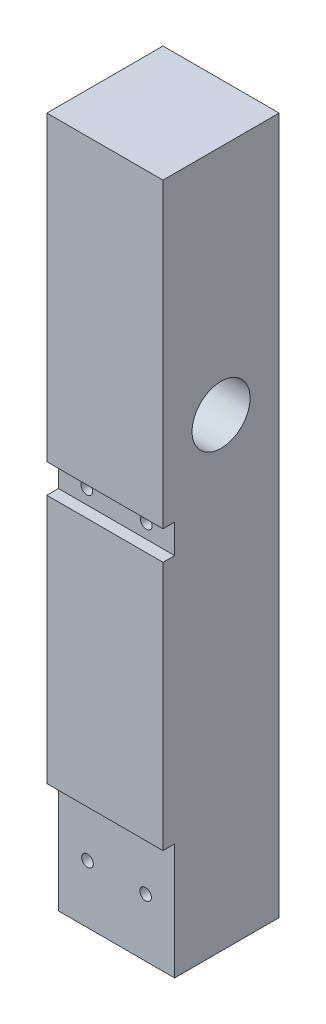
SolidWorks part; units mm, degrees
ref_plane "Front Plane" through (0, 0, 0) normal (0, 0, 1) x (1, 0, 0)
ref_plane "Top Plane" through (0, 0, 0) normal (0, 1, 0) x (1, 0, 0)
ref_plane "Right Plane" through (0, 0, 0) normal (1, 0, 0) x (0, 0, -1)
sketch "Sketch1" plane through (0, 0, 0) normal (1, 0, 0) x (0, 0, -1)
  line L0 (0, 55) -> (0, -55) construction
  line L1 (0, 120) -> (20, 120)
  line L2 (0, 120) -> (0, 0)
  line L3 (0, 0) -> (20, 0)
  line L4 (20, 120) -> (20, 0)
  line L5 (55, 0) -> (-55, 0) construction
  circle A2 centre (10, 80) radius 2.5
  dimension "D3" = 5
  dimension "D4" = 40
  dimension "D5" = 10
  dimension "D1" = 20
  dimension "D2" = 120
extrude "Boss-Extrude2" add sketch "Sketch1" against normal blind 20
ref_plane "Plane1" through (0, 0, 0) normal (1, 0, 0) x (0, 0, -1)
sketch "Sketch10" plane through (0, 0, 0) normal (1, 0, 0) x (0, 0, -1)
  circle A0 centre (10, 80) radius 5
  dimension "D1" = 10
extrude "Cut-Extrude1" cut sketch "Sketch10" against normal blind 10
ref_plane "Plane2" through (0, 0, 0) normal (0, 0, 1) x (1, 0, 0)
sketch "Sketch11" plane through (0, 0, 0) normal (0, 0, 1) x (1, 0, 0)
  line L0 (-10, 120) -> (-10, 0)
  line L1 (-20, 120) -> (0, 120) construction
  line L2 (11, 0) -> (-11, 0) construction
  line L3 (-20, 120) -> (-20, 0) construction
  line L4 (-20, 0) -> (0, 0) construction
  circle A0 centre (-15, 10) radius 1
  circle A1 centre (-5, 10) radius 1
  dimension "D1" = 2
  dimension "D2" = 5
  dimension "D3" = 10
extrude "Cut-Extrude2" cut sketch "Sketch11" against normal through all contours A0 | A1
ref_plane "Plane3" through (0, 0, -20) normal (0, 0, -1) x (-1, 0, 0)
sketch "Sketch12" plane through (0, 0, -20) normal (0, 0, -1) x (-1, 0, 0)
  circle A0 centre (5, 10) radius 2
  circle A1 centre (15, 10) radius 2
  dimension "D1" = 4
  dimension "D2" = 4
extrude "Cut-Extrude3" cut sketch "Sketch12" against normal blind 5
ref_plane "Plane4" through (0, 0, -20) normal (0, 0, -1) x (-1, 0, 0)
sketch "Sketch13" plane through (0, 0, -20) normal (0, 0, -1) x (-1, 0, 0)
  line L0 (10, 120) -> (10, 0)
  line L1 (20, 120) -> (0, 120) construction
  line L2 (11, 0) -> (-11, 0) construction
  circle A0 centre (4.8805, 65.5) radius 1
  circle A1 centre (15.1195, 65.5) radius 1
  dimension "D1" = 2
  dimension "D2" = 65.5
extrude "Cut-Extrude4" cut sketch "Sketch13" against normal through all contours A0 | A1
ref_plane "Plane5" through (0, 0, -20) normal (0, 0, -1) x (-1, 0, 0)
sketch "Sketch14" plane through (0, 0, -20) normal (0, 0, -1) x (-1, 0, 0)
  circle A0 centre (4.8805, 65.5) radius 2
  circle A1 centre (15.1195, 65.5) radius 2
  dimension "D1" = 4
  dimension "D2" = 4
extrude "Cut-Extrude5" cut sketch "Sketch14" against normal blind 5
ref_plane "Plane6" through (0, 0, 0) normal (0, 0, 1) x (1, 0, 0)
sketch "Sketch16" plane through (0, 0, 0) normal (0, 0, 1) x (1, 0, 0)
  line L0 (11, 0) -> (-11, 0) construction
  line L1 (-20, 68) -> (0, 68)
  line L2 (-20, 68) -> (-20, 63)
  line L3 (-20, 63) -> (0, 63)
  line L4 (0, 68) -> (0, 63)
  line L5 (-20, 68) -> (0, 63) construction
  line L6 (-20, 63) -> (0, 68) construction
  line L7 (-20, 120) -> (-20, 0) construction
  line L8 (0, -11) -> (0, 11) construction
  line L9 (-20, 20) -> (0, 20)
  line L10 (-20, 20) -> (-20, 0)
  line L11 (-20, 0) -> (0, 0)
  line L12 (0, 20) -> (0, 0)
  line L13 (-20, 20) -> (0, 0) construction
  line L14 (-20, 0) -> (0, 20) construction
  point P0 (-10, 65.5)
  point P9 (-10, 10)
  dimension "D1" = 65.5
  dimension "D2" = 10
  dimension "D3" = 5
  dimension "D4" = 20
  dimension "D5" = 10
extrude "Cut-Extrude6" cut sketch "Sketch16" against normal blind 2
